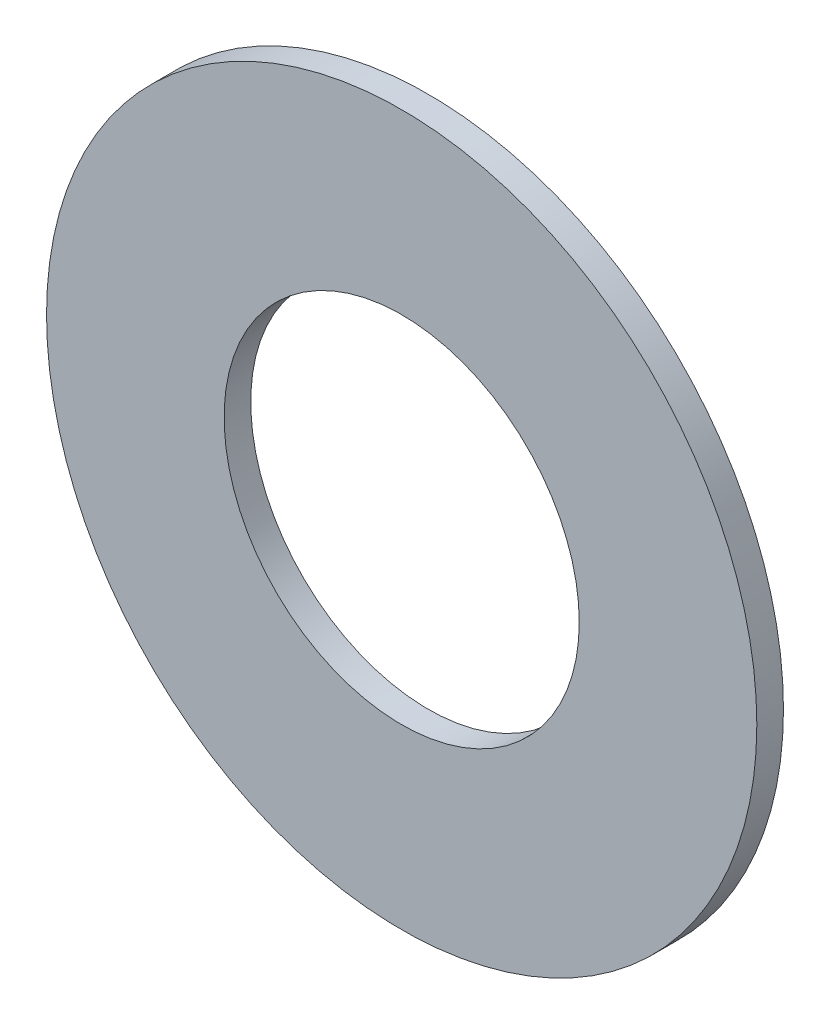
SolidWorks part; units mm, degrees
ref_plane "Front Plane" through (0, 0, 0) normal (1, 0, 0) x (0, 1, 0)
ref_plane "Top Plane" through (0, 0, 0) normal (0, 0, 1) x (0, 1, 0)
ref_plane "Right Plane" through (0, 0, 0) normal (0, 1, 0) x (-1, 0, 0)
sketch "Sketch1" plane through (0, 0, 0) normal (0, 0, 1) x (0, 1, 0)
  circle A0 centre (0, 0) radius 8
  circle A1 centre (0, 0) radius 16
  dimension "D1" = 16
  dimension "D2" = 32
extrude "Boss-Extrude1" add sketch "Sketch1" along normal blind 1.2
